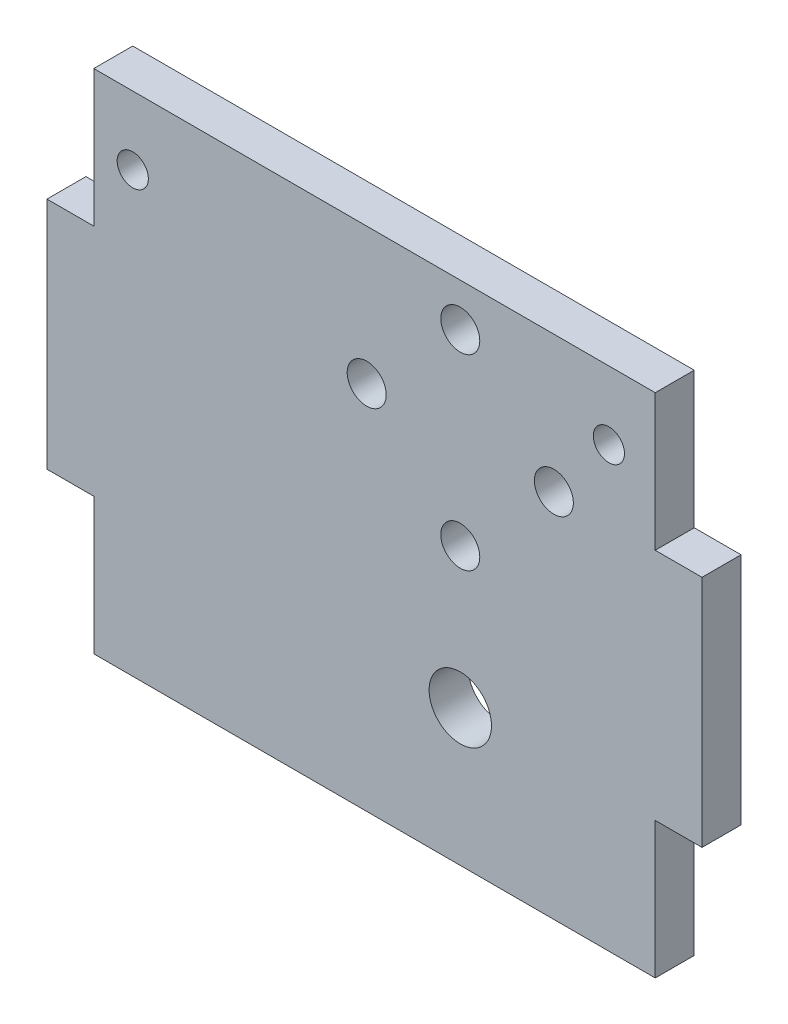
SolidWorks part; units mm, degrees
ref_plane "Front Plane" through (0, 0, 0) normal (0, 0, 1) x (1, 0, 0)
ref_plane "Top Plane" through (0, 0, 0) normal (0, 1, 0) x (1, 0, 0)
ref_plane "Right Plane" through (0, 0, 0) normal (1, 0, 0) x (0, 0, -1)
sketch "Sketch2" plane through (0, 0, 0) normal (0, 0, 1) x (1, 0, 0)
  line L1 (0, 0) -> (50, 0)
  line L2 (0, 0) -> (0, 65)
  line L3 (0, 65) -> (50, 65)
  line L4 (50, 0) -> (50, 65)
  circle A19 centre (25, 59.5) radius 2
  circle A20 centre (13, 47.5) radius 2
  circle A21 centre (37, 47.5) radius 2
  circle A23 centre (25, 17.5) radius 4
extrude "Boss-Extrude1" add sketch "Sketch2" along normal blind 5
sketch "Sketch4" plane through (0, 0, 5) normal (0, 0, 1) x (1, 0, 0)
  line L0 (50, 65) -> (71, 65)
  line L1 (71, 65) -> (71, 0)
  line L2 (71, 0) -> (50, 0)
  line L3 (50, 0) -> (50, 65)
  line L4 (25, 59.5) -> (25, 17.5)
  line L5 (0, 0) -> (0, 65)
  line L6 (-21, 0) -> (0, 0)
  line L7 (-21, 65) -> (-21, 0)
  line L8 (0, 65) -> (-21, 65)
  line M1 (0, 65) -> (0, 0)
extrude "Boss-Extrude3" add sketch "Sketch4" against normal up to surface (5 mm away) contours L8 L7 L6 M1 up to face at (15, 47.5, 0)
sketch "Sketch5" plane through (0, 0, 0) normal (0, 0, -1) x (-1, 0, 0)
  line L0 (21, 65) -> (22, 65)
  line L1 (22, 65) -> (22, 0)
  line L2 (22, 0) -> (21, 0)
  line L3 (21, 0) -> (21, 65)
extrude "Boss-Extrude4" add sketch "Sketch5" against normal up to surface (5 mm away) up to face at (14.5, 32.5, 5)
sketch "Sketch6" plane through (0, 0, 5) normal (0, 0, 1) x (1, 0, 0)
  line L0 (-22, 32.5) -> (-22, 47.5)
  line L1 (-22, 65) -> (-22, 0) construction
  line L2 (-22, 32.5) -> (-22, 17.5)
  line L3 (-22, 17.5) -> (-28, 17.5)
  line L4 (-28, 17.5) -> (-28, 47.5)
  line L5 (-28, 47.5) -> (-22, 47.5)
  line L6 (14, 65) -> (14, 11.5794)
  line L7 (50, 65) -> (-22, 65) construction
  line L8 (56, 47.5) -> (50, 47.5)
  line L9 (56, 17.5) -> (56, 47.5)
  line L10 (50, 17.5) -> (56, 17.5)
  line L11 (50, 32.5) -> (50, 17.5)
  line L12 (50, 32.5) -> (50, 47.5)
  line M8 (-22, 65) -> (-22, 0)
  line M10 (50, 0) -> (50, 65)
extrude "Boss-Extrude5" add sketch "Sketch6" against normal up to surface (5 mm away) contours L5 L4 L3 M8 | L10 L9 L8 M10 up to face at (15, 47.5, 0)
sketch "Sketch7" plane through (0, 0, 5) normal (0, 0, 1) x (1, 0, 0)
  circle A1 centre (25, 35.5) radius 2
extrude "Cut-Extrude1" cut sketch "Sketch7" against normal blind 59
sketch "Sketch8" plane through (0, 0, 5) normal (0, 0, 1) x (1, 0, 0)
  line L0 (50, 56.25) -> (44.0556, 56.25)
  line L1 (50, 47.5) -> (50, 65) construction
  line L2 (-22, 56.25) -> (-17, 56.25)
  line L3 (-22, 65) -> (-22, 47.5) construction
  circle A0 centre (-17, 56.25) radius 1.5
  circle A1 centre (44.0556, 56.25) radius 1.5
extrude "Cut-Extrude2" cut sketch "Sketch8" against normal blind 10
sketch "Sketch9" plane through (0, 0, 5) normal (0, 0, 1) x (1, 0, 0)
  circle A0 centre (-17, 56.25) radius 2
  circle A1 centre (44.0556, 56.25) radius 2
extrude "Cut-Extrude3" cut sketch "Sketch9" against normal blind 10
sketch "Sketch10" plane through (0, 0, 5) normal (0, 0, 1) x (1, 0, 0)
  circle A0 centre (25, 59.5) radius 2.5
  circle A1 centre (25, 35.5) radius 2.5
  circle A2 centre (13, 47.5) radius 2.5
  circle A3 centre (37, 47.5) radius 2.5
extrude "Cut-Extrude4" cut sketch "Sketch10" against normal blind 10
